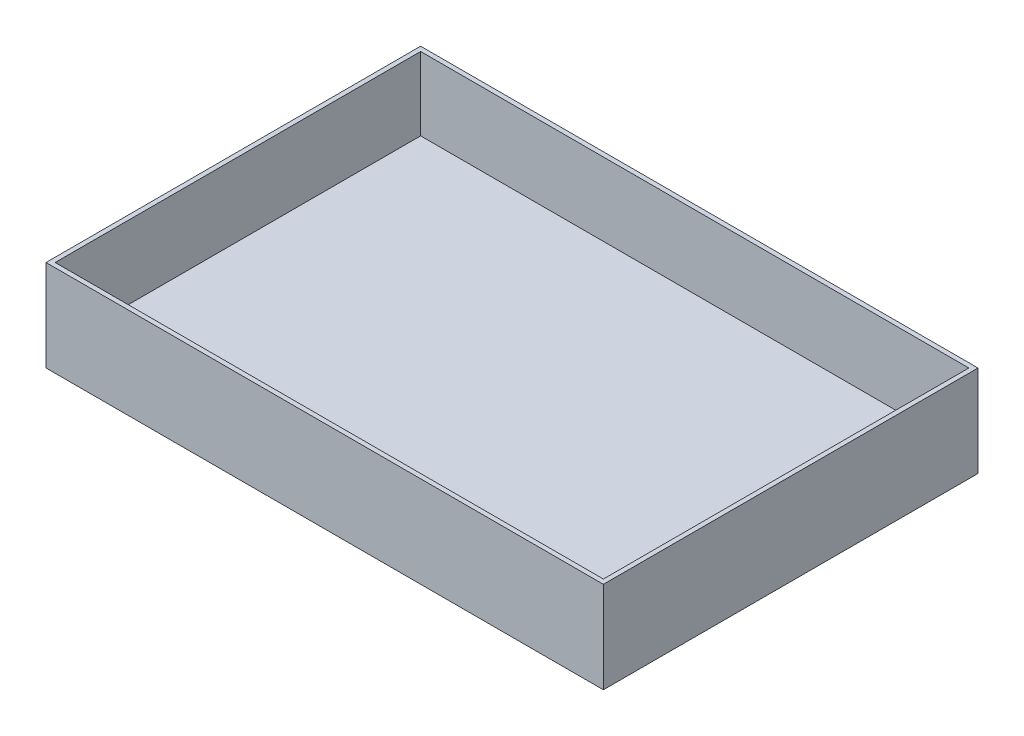
SolidWorks part; units mm, degrees
ref_plane "Plano frontal" through (0, 0, 0) normal (0, 0, 1) x (1, 0, 0)
ref_plane "Plano superior" through (0, 0, 0) normal (0, 1, 0) x (1, 0, 0)
ref_plane "Plano direito" through (0, 0, 0) normal (1, 0, 0) x (0, 0, -1)
sketch "Esboço4" plane through (0, 0, 0) normal (0, 1, 0) x (1, 0, 0)
  line L1 (-30.5, 20.5) -> (30.5, 20.5)
  line L2 (-30.5, 20.5) -> (-30.5, -20.5)
  line L3 (-30.5, -20.5) -> (30.5, -20.5)
  line L4 (30.5, 20.5) -> (30.5, -20.5)
  line L5 (-30.5, 20.5) -> (30.5, -20.5) construction
  line L6 (-30.5, -20.5) -> (30.5, 20.5) construction
  point P0 (0, 0)
  dimension "D1" = 61
  dimension "D2" = 41
extrude "Ressalto-extrusão1" add sketch "Esboço4" along normal blind 10 contours L1 L4 L3 L2
sketch "Esboço5" plane through (0, 10, 0) normal (0, 1, 0) x (1, 0, 0)
  line L1 (-30, 20) -> (30, 20)
  line L2 (-30, 20) -> (-30, -20)
  line L3 (-30, -20) -> (30, -20)
  line L4 (30, 20) -> (30, -20)
  line L5 (-30, 20) -> (30, -20) construction
  line L6 (-30, -20) -> (30, 20) construction
  point P0 (0, 0)
  dimension "D1" = 60
  dimension "D2" = 40
extrude "Corte-extrusão1" cut sketch "Esboço5" against normal blind 8
